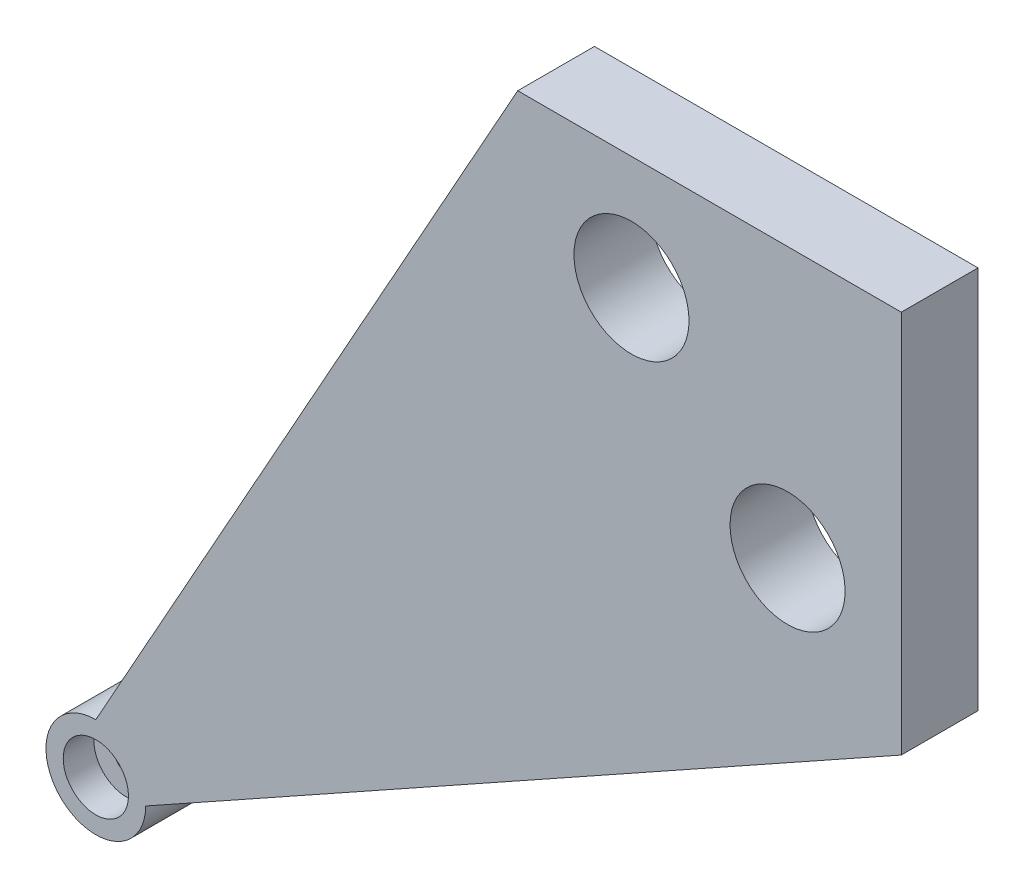
SolidWorks part; units mm, degrees
ref_plane "Plano frontal" through (0, 0, 0) normal (0, 0, 1) x (1, 0, 0)
ref_plane "Plano superior" through (0, 0, 0) normal (0, 1, 0) x (1, 0, 0)
ref_plane "Plano direito" through (0, 0, 0) normal (1, 0, 0) x (0, 0, -1)
sketch "Esboço3" plane through (0, 0, 0) normal (0, 0, 1) x (1, 0, 0)
  line L0 (-62.966, 0) -> (106.6858, 0) construction
  line L1 (0, 69.7378) -> (0, -73.302) construction
  line L2 (0, 50) -> (98.5, 105)
  line L3 (0, 0) -> (50, 0)
  line L4 (0, 0) -> (0, 50)
  line L7 (50, 0) -> (105, 98.5)
  arc A0 (105, 98.5) -> (98.5, 105) centre (105, 105) ccw
  dimension "D4" = 105
  dimension "D5" = 13
  dimension "D3" = 105
extrude "Ressalto-extrusão2" add sketch "Esboço3" along normal mid plane 10
sketch "Esboço4" plane through (0, 0, 5) normal (0, 0, 1) x (1, 0, 0)
  circle A0 centre (105, 105) radius 4.25
  arc A1 (105, 98.5) -> (98.5, 105) centre (105, 105) ccw construction
  dimension "D1" = 8.5
extrude "Corte-extrusão1" cut sketch "Esboço4" against normal blind 4 contours A0
sketch "Esboço5" plane through (0, 0, 1) normal (0, 0, 1) x (1, 0, 0)
  circle A0 centre (105, 105) radius 1.5
  circle A1 centre (105, 105) radius 4.25 construction
extrude "Corte-extrusão2" cut sketch "Esboço5" against normal through all
sketch "Esboço6" plane through (0, 0, 5) normal (0, 0, 1) x (1, 0, 0)
  line L0 (-26.6702, 0) -> (72.5742, 0) construction
  line L1 (0, 62.2144) -> (0, -11.4301) construction
  line L2 (0, 50) -> (63.2897, 50) construction
  line L3 (50, 0) -> (50, 50) construction
  line L4 (0, 50) -> (14.8256, 35.1744) construction
  line L5 (14.8256, 35.1744) -> (35.1744, 14.8256) construction
  line L6 (35.1744, 14.8256) -> (50, 0) construction
  line L7 (0, 0) -> (50, 50) construction
  circle A0 centre (14.8256, 35.1744) radius 7.5
  circle A1 centre (35.1744, 14.8256) radius 7.5
  point P16 (0, 0)
  dimension "D1" = 15
  dimension "D2" = 15
extrude "Corte-extrusão3" cut sketch "Esboço6" against normal through all
mirror "Espelhar1" about plane through (0, 0, 5) normal (0, 1, 0) of bodies 105
mirror "Espelhar2" about plane through (0, 0, 5) normal (1, 0, 0) of bodies 106 105
delete or keep bodies "Corpo-Excluir/Manter 1" type delete bodies bodies 108
delete or keep bodies "Corpo-Excluir/Manter 2" type delete bodies bodies 105
delete or keep bodies "Corpo-Excluir/Manter 4" type delete bodies bodies 106
